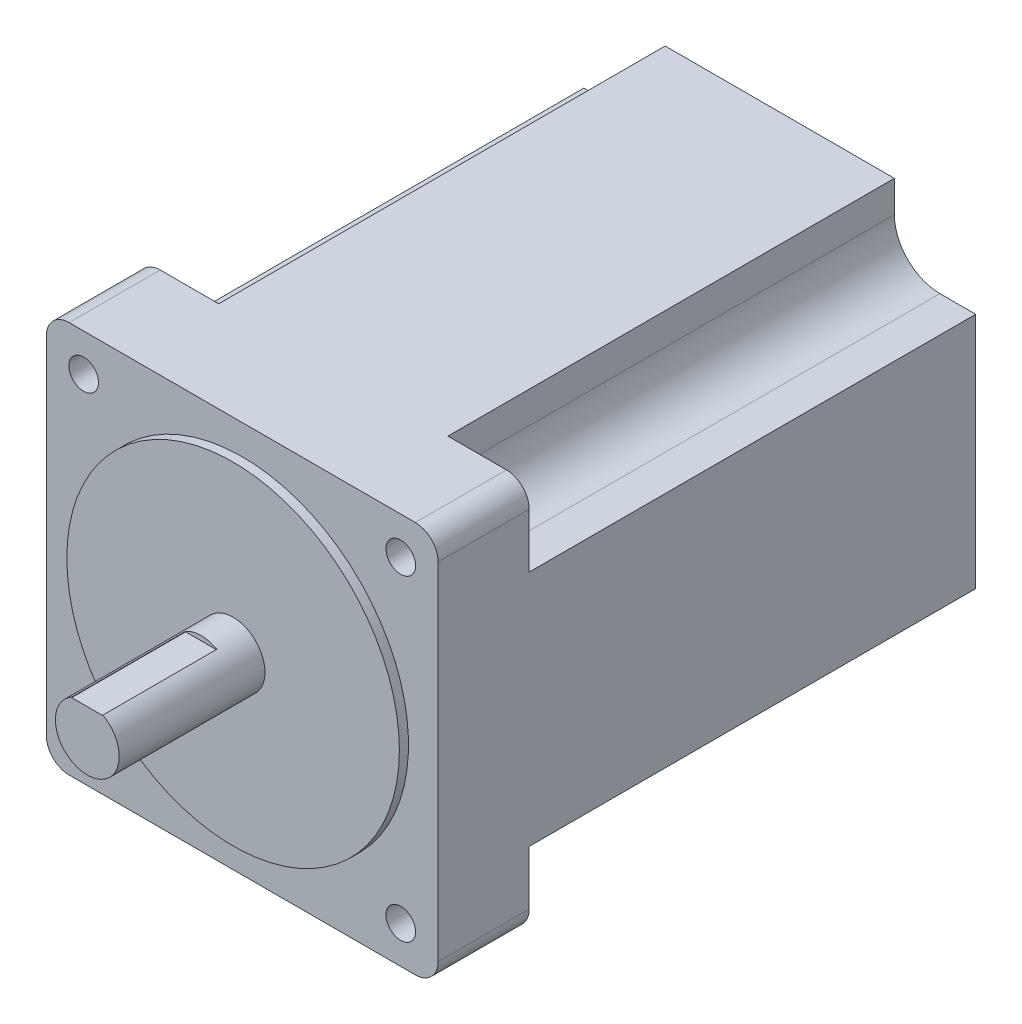
SolidWorks part; units mm, degrees
ref_plane "前视基准面" through (0, 0, 0) normal (0, 0, 1) x (1, 0, 0)
ref_plane "上视基准面" through (0, 0, 0) normal (0, 1, 0) x (1, 0, 0)
ref_plane "右视基准面" through (0, 0, 0) normal (1, 0, 0) x (0, 0, -1)
sketch "草图1" plane through (0, 0, 0) normal (0, 0, 1) x (1, 0, 0)
  line L1 (0, 0) -> (86, 0)
  line L2 (0, 0) -> (0, 86)
  line L3 (0, 86) -> (86, 86)
  line L4 (86, 0) -> (86, 86)
  dimension "D1" = 86
  dimension "D2" = 86
extrude "凸台-拉伸1" add sketch "草图1" along normal blind 118
fillet "圆角1" radius 5 4 edges at (86, 0, 59) (0, 0, 59) (0, 86, 59) (86, 86, 59)
sketch "草图2" plane through (0, 0, 118) normal (0, 0, 1) x (1, 0, 0)
  line L0 (43, 86) -> (43, 0) construction
  line L1 (81, 86) -> (5, 86) construction
  line L2 (5, 0) -> (81, 0) construction
  line L3 (43, 0) -> (43, 43) construction
  circle A0 centre (43, 43) radius 36.5
  dimension "D1" = 73
extrude "凸台-拉伸2" add sketch "草图2" along normal blind 2
sketch "草图3" plane through (0, 0, 120) normal (0, 0, 1) x (1, 0, 0)
  circle A0 centre (43, 43) radius 7
  dimension "D1" = 14
extrude "凸台-拉伸3" add sketch "草图3" along normal blind 32
sketch "草图4" plane through (0, 0, 152) normal (0, 0, 1) x (1, 0, 0)
  line L0 (43, 43) -> (43, 86) construction
  line L1 (81, 86) -> (5, 86) construction
  line L3 (39.576, 52.2762) -> (46.424, 52.2762)
  line L4 (39.576, 52.2762) -> (39.576, 49)
  line L5 (39.576, 49) -> (46.424, 49)
  line L6 (46.424, 52.2762) -> (46.424, 49)
  dimension "D1" = 6
extrude "切除-拉伸1" cut sketch "草图4" against normal blind 25
sketch "草图5" plane through (0, 0, 118) normal (0, 0, 1) x (1, 0, 0)
  line L0 (43, 86) -> (43, 0) construction
  line L1 (81, 86) -> (5, 86) construction
  line L2 (5, 0) -> (81, 0) construction
  line L3 (43, 0) -> (43, 43) construction
  line L4 (43, 43) -> (90.7226, 43) construction
  circle A0 centre (8.2, 77.8) radius 3.25
  circle A1 centre (77.8, 77.8) radius 3.25
  circle A2 centre (77.8, 8.2) radius 3.25
  circle A3 centre (8.2, 8.2) radius 3.25
  dimension "D1" = 6.5
  dimension "D2" = 69.6
  dimension "D3" = 69.6
extrude "切除-拉伸2" cut sketch "草图5" against normal through all
sketch "草图6" plane through (0, 0, 0) normal (0, 0, -1) x (-1, 0, 0)
  line L0 (-81, 86) -> (-5, 86) construction
  line L1 (-68.1565, 86) -> (-93.0252, 86)
  line L2 (-68.1565, 86) -> (-68.1565, 79.0776)
  line L3 (-78.1565, 69.0776) -> (-93.0252, 69.0776)
  line L4 (-93.0252, 86) -> (-93.0252, 69.0776)
  line L5 (-43, 86) -> (-43, 0) construction
  line L6 (-5, 0) -> (-81, 0) construction
  line L7 (-43, 0) -> (-43, 43) construction
  line L8 (-43, 43) -> (14.5654, 43) construction
  line L9 (-17.8435, 86) -> (-17.8435, 79.0776)
  line L10 (-17.8435, 86) -> (7.0252, 86)
  line L11 (7.0252, 86) -> (7.0252, 69.0776)
  line L12 (-7.8435, 69.0776) -> (7.0252, 69.0776)
  line L13 (-7.8435, 16.9224) -> (7.0252, 16.9224)
  line L14 (7.0252, 0) -> (7.0252, 16.9224)
  line L15 (-17.8435, 0) -> (7.0252, 0)
  line L16 (-17.8435, 0) -> (-17.8435, 6.9224)
  line L17 (-68.1565, 0) -> (-68.1565, 6.9224)
  line L18 (-68.1565, 0) -> (-93.0252, 0)
  line L19 (-93.0252, 0) -> (-93.0252, 16.9224)
  line L20 (-78.1565, 16.9224) -> (-93.0252, 16.9224)
  arc A0 (-78.1565, 69.0776) -> (-68.1565, 79.0776) centre (-78.1565, 79.0776) ccw
  arc A1 (-7.8435, 69.0776) -> (-17.8435, 79.0776) centre (-7.8435, 79.0776) cw
  arc A2 (-7.8435, 16.9224) -> (-17.8435, 6.9224) centre (-7.8435, 6.9224) ccw
  arc A3 (-78.1565, 16.9224) -> (-68.1565, 6.9224) centre (-78.1565, 6.9224) cw
  dimension "D1" = 10
extrude "切除-拉伸3" cut sketch "草图6" against normal blind 98
